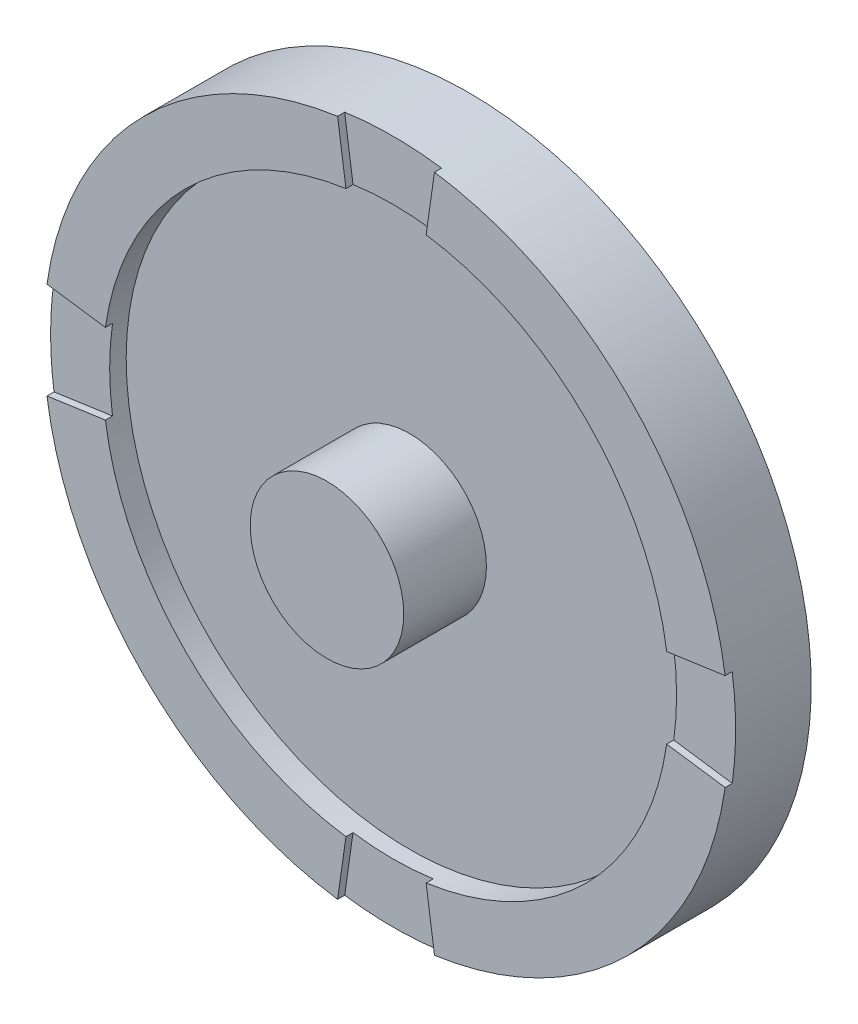
SolidWorks part; units mm, degrees
ref_plane "Front" through (0, 0, 0) normal (0, 0, 1) x (1, 0, 0)
ref_plane "Top" through (0, 0, 0) normal (0, 1, 0) x (1, 0, 0)
ref_plane "Right" through (0, 0, 0) normal (1, 0, 0) x (0, 0, -1)
sketch "Sketch1" plane through (0, 0, 0) normal (0, 0, 1) x (1, 0, 0)
  circle A0 centre (0, 0) radius 24
extrude "Extrude1" add sketch "Sketch1" along normal blind 5
sketch "Sketch2" plane through (0, 0, 5) normal (0, 0, 1) x (1, 0, 0)
  circle A0 centre (0, 0) radius 6.5
extrude "Extrude2" add sketch "Sketch2" along normal blind 7
sketch "Sketch3" plane through (0, 0, 0) normal (0, 0, -1) x (-1, 0, 0)
  circle A0 centre (0, 0) radius 24
  circle A1 centre (0, 0) radius 29
extrude "Extrude3" add sketch "Sketch3" against normal blind 7
sketch "Sketch4" plane through (0, 0, 7) normal (0, 0, 1) x (1, 0, 0)
  line L0 (33.3375, 4.7625) -> (-33.3375, -4.7625) construction
  line L1 (33.3375, -4.7625) -> (-33.3375, 4.7625) construction
  line L2 (4.7625, 33.3375) -> (-4.7625, -33.3375) construction
  line L3 (-4.7625, 33.3375) -> (4.7625, -33.3375) construction
  line L4 (3.3941, 23.7588) -> (4.1012, 28.7085)
  line L5 (-3.3941, 23.7588) -> (-4.1012, 28.7085)
  line L6 (23.7588, -3.3941) -> (28.7085, -4.1012)
  line L7 (23.7588, 3.3941) -> (28.7085, 4.1012)
  line L8 (3.3941, -23.7588) -> (4.1012, -28.7085)
  line L9 (-3.3941, -23.7588) -> (-4.1012, -28.7085)
  line L10 (-23.7588, -3.3941) -> (-28.7085, -4.1012)
  line L11 (-23.7588, 3.3941) -> (-28.7085, 4.1012)
  arc A0 (24, 0) -> (23.7588, 3.3941) centre (0, 0) ccw
  circle A2 centre (0, 0) radius 24 construction
  arc A3 (24, 0) -> (23.7588, -3.3941) centre (0, 0) cw
  arc A4 (29, 0) -> (28.7085, 4.1012) centre (0, 0) ccw
  circle A5 centre (0, 0) radius 29 construction
  arc A6 (29, 0) -> (28.7085, -4.1012) centre (0, 0) cw
  arc A7 (0, 24) -> (3.3941, 23.7588) centre (0, 0) cw
  arc A8 (0, 24) -> (-3.3941, 23.7588) centre (0, 0) ccw
  arc A9 (0, 29) -> (4.1012, 28.7085) centre (0, 0) cw
  arc A10 (0, 29) -> (-4.1012, 28.7085) centre (0, 0) ccw
  arc A11 (-24, 0) -> (-23.7588, 3.3941) centre (0, 0) cw
  arc A12 (-24, 0) -> (-23.7588, -3.3941) centre (0, 0) ccw
  arc A13 (-29, 0) -> (-28.7085, 4.1012) centre (0, 0) cw
  arc A14 (-29, 0) -> (-28.7085, -4.1012) centre (0, 0) ccw
  arc A15 (0, -24) -> (3.3941, -23.7588) centre (0, 0) ccw
  arc A16 (0, -24) -> (-3.3941, -23.7588) centre (0, 0) cw
  arc A17 (0, -29) -> (4.1012, -28.7085) centre (0, 0) ccw
  arc A18 (0, -29) -> (-4.1012, -28.7085) centre (0, 0) cw
extrude "Cut-Extrude1" cut sketch "Sketch4" against normal blind 0.6
